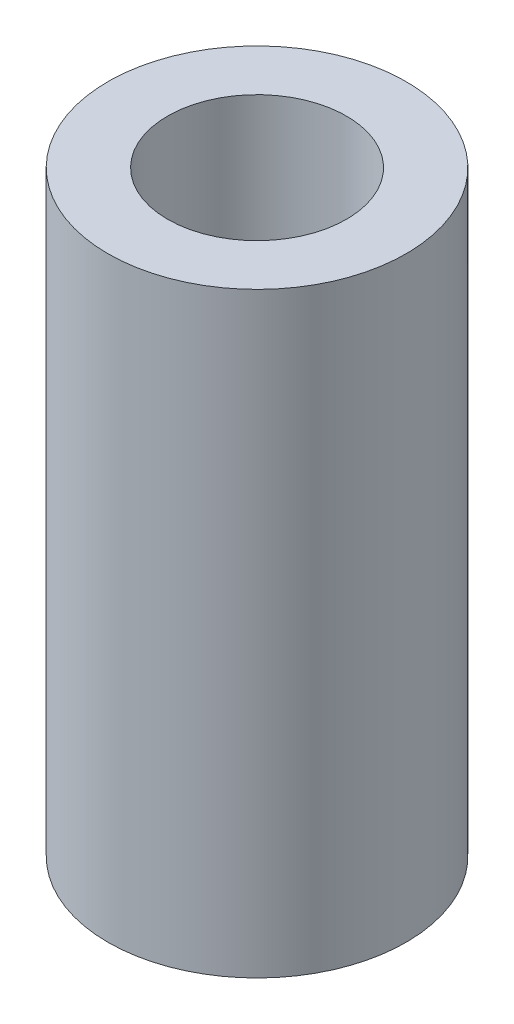
SolidWorks part; units mm, degrees
material "ABS"
ref_plane "Front Plane" through (0, 0, 0) normal (0, 0, 1) x (1, 0, 0)
ref_plane "Top Plane" through (0, 0, 0) normal (0, 1, 0) x (1, 0, 0)
ref_plane "Right Plane" through (0, 0, 0) normal (1, 0, 0) x (0, 0, -1)
sketch "Sketch1" plane through (0, 0, 0) normal (0, 1, 0) x (1, 0, 0)
  circle A0 centre (0, 0) radius 3.81
  circle A1 centre (0, 0) radius 6.35
  dimension "D1" = 7.62
  dimension "D3" = 12.7
extrude "Boss-Extrude1" add sketch "Sketch1" along normal blind 25.4
